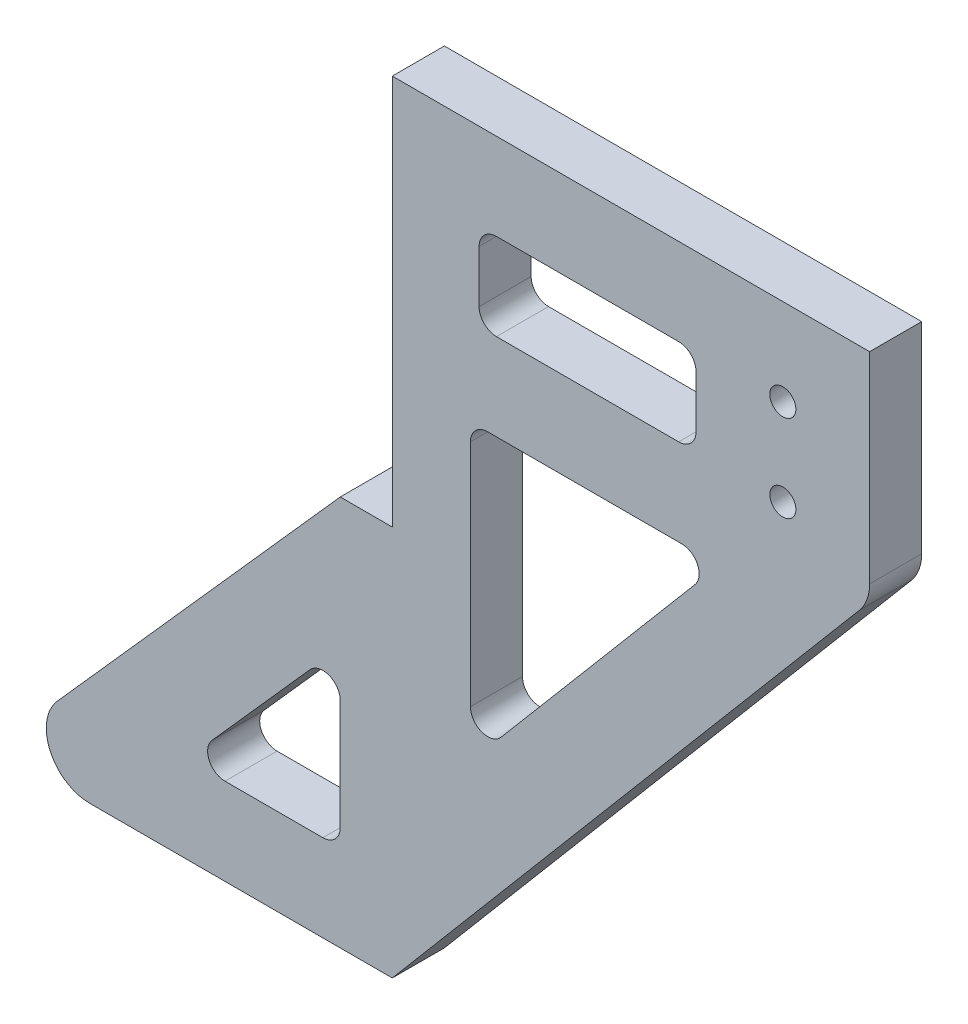
SolidWorks part; units mm, degrees
ref_plane "Front Plane" through (0, 0, 0) normal (0, 0, 1) x (1, 0, 0)
ref_plane "Top Plane" through (0, 0, 0) normal (0, 1, 0) x (1, 0, 0)
ref_plane "Right Plane" through (0, 0, 0) normal (1, 0, 0) x (0, 0, -1)
sketch "Sketch1" plane through (0, 0, 0) normal (0, 0, 1) x (1, 0, 0)
  line L1 (0, 0) -> (55, 0)
  line L4 (0, 0) -> (0, -45)
  line L5 (0, -45) -> (-6, -45)
  line L6 (-6, -45) -> (-46, -90)
  line L9 (-46, -90) -> (0, -90)
  line L11 (55, 0) -> (55, -25)
  line L15 (0, -90) -> (55, -25)
  dimension "D1" = 45
  dimension "D2" = 55
  dimension "D3" = 6
  dimension "D4" = 90
  dimension "D6" = 46
  dimension "D7" = 25
extrude "Boss-Extrude1" add sketch "Sketch1" along normal blind 6
sketch "Sketch4" plane through (0, 0, 6) normal (0, 0, 1) x (1, 0, 0)
  line L1 (9, -30) -> (9, -63.8824)
  line L3 (37.6697, -30) -> (9, -63.8824)
  line L4 (0, -90) -> (55, -25) construction
  line L6 (0, 0) -> (0, -45) construction
  line L8 (-6, -60.052) -> (-23.7316, -80)
  line L9 (-23.7316, -80) -> (-6, -80)
  line L10 (-6, -80) -> (-6, -60.052)
  line L11 (-6, -45) -> (-46, -90) construction
  line L13 (-46, -90) -> (0, -90) construction
  line L14 (10, -20) -> (35, -20)
  line L15 (55, 0) -> (0, 0) construction
  line L16 (9, -30) -> (37.6697, -30)
  line L17 (0, 0) -> (55, 0) construction
  line L18 (55, 0) -> (55, -25) construction
  line L19 (10, -20) -> (10, -10)
  line L20 (10, -10) -> (35, -10)
  line L21 (35, -20) -> (35, -10)
  circle A0 centre (45, -20) radius 1.5
  circle A1 centre (45, -10) radius 1.5
  dimension "D8" = 3
  dimension "D1" = 9
  dimension "D2" = 10
  dimension "D3" = 10
  dimension "D4" = 30
  dimension "D5" = 10
  dimension "D6" = 6
  dimension "D7" = 10
  dimension "D9" = 10
  dimension "D10" = 20
  dimension "D11" = 10
  dimension "D12" = 10
  dimension "D13" = 10
  dimension "D14" = 20
extrude "Cut-Extrude2" cut sketch "Sketch4" against normal through all both and the other way through all
fillet "Fillet1" radius 2 7 edges at (-23.7316, -80, 3) (-6, -80, 3) (-6, -60.052, 3) (10, -20, 3) (35, -20, 3) (10, -10, 3) (35, -10, 3)
fillet "Fillet2" radius 2 3 edges at (9, -63.8824, 3) (9, -30, 3) (37.6697, -30, 3)
fillet "Fillet3" radius 5 2 edges at (55, -25, 3) (-46, -90, 3)
ref_plane "Plane1" through (0, 0, 0) normal (0, 1, 0) x (1, 0, 0)
sketch "Sketch5" plane through (0, 0, 0) normal (0, 1, 0) x (1, 0, 0)
  line L0 (0, -3) -> (55, -3) construction
  line L1 (0, -6) -> (0, 0) construction
  line L2 (55, -6) -> (55, 0) construction
